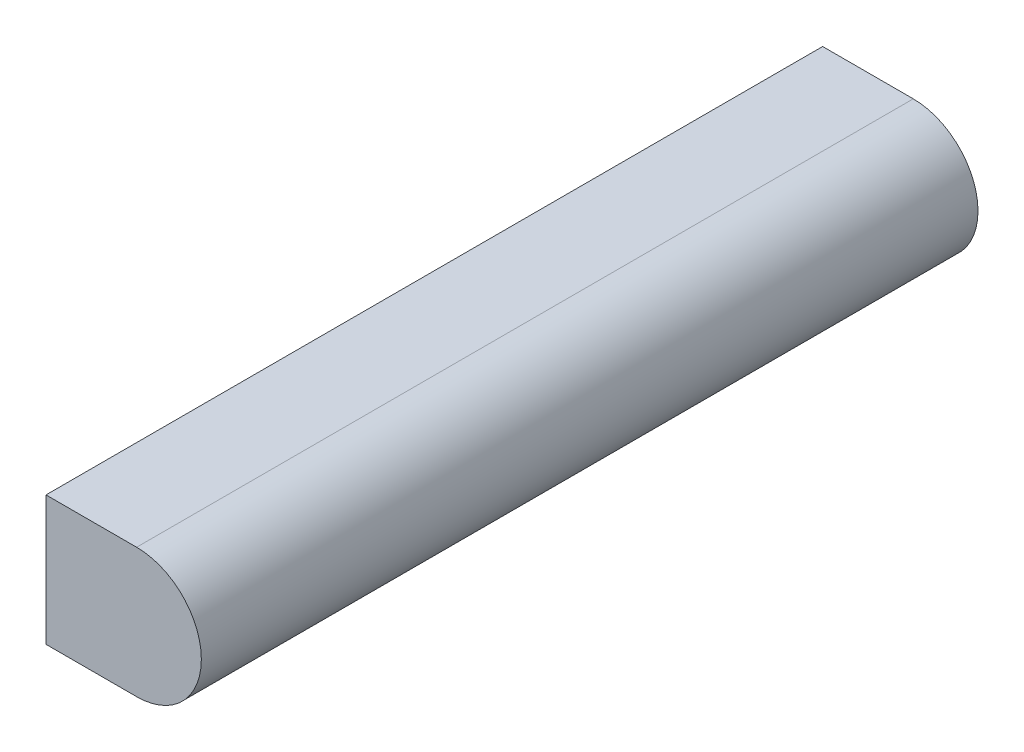
SolidWorks part; units mm, degrees
ref_plane "Front Plane" through (0, 0, 0) normal (0, 0, 1) x (1, 0, 0)
ref_plane "Top Plane" through (0, 0, 0) normal (0, 1, 0) x (1, 0, 0)
ref_plane "Right Plane" through (0, 0, 0) normal (1, 0, 0) x (0, 0, -1)
sketch "Sketch3" plane through (0, 0, 38.1) normal (0, 0, 1) x (1, 0, 0)
  line L2 (3.177, -3.174) -> (7.621, -3.174)
  line L3 (3.175, 3.176) -> (7.621, 3.176)
  line L4 (3.175, 3.176) -> (3.177, -3.174)
  arc A1 (7.621, -3.174) -> (7.621, 3.176) centre (7.621, 0.001) ccw
extrude "Boss-Extrude1" add sketch "Sketch3" against normal blind 38.1
